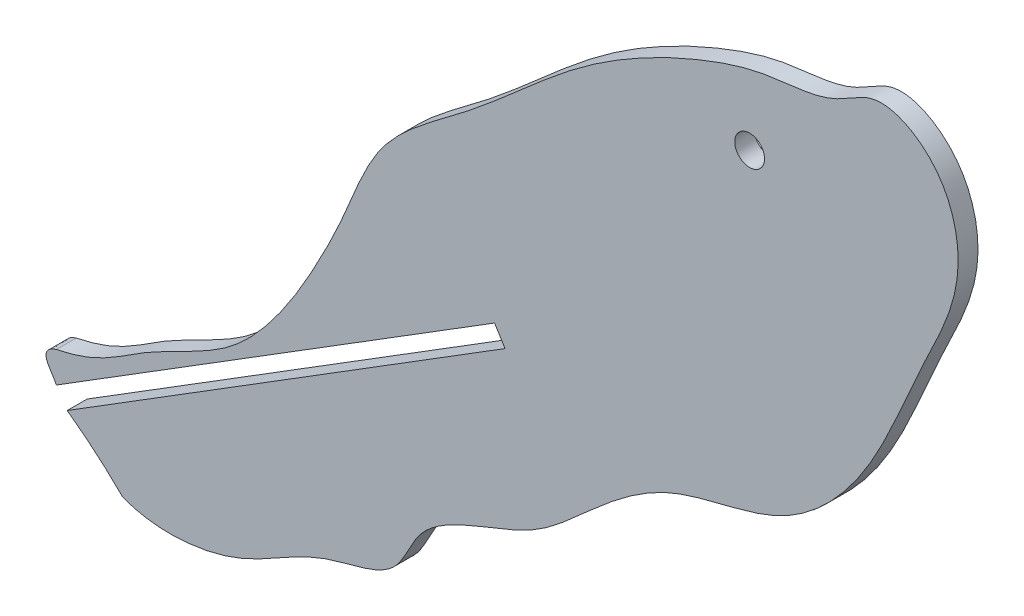
SolidWorks part; units mm, degrees
ref_plane "Front Plane" through (0, 0, 0) normal (0, 0, 1) x (1, 0, 0)
ref_plane "Top Plane" through (0, 0, 0) normal (0, 1, 0) x (1, 0, 0)
ref_plane "Right Plane" through (0, 0, 0) normal (1, 0, 0) x (0, 0, -1)
sketch "Sketch1" plane through (0, 0, 0) normal (0, 0, 1) x (1, 0, 0)
  line L0 (180.8536, 209.2521) -> (904.2678, 209.2521) construction
  line L1 (40.7681, 184.4531) -> (114.0777, 230.0867)
  line L2 (114.0777, 230.0867) -> (115.7555, 227.3912)
  line L3 (115.7555, 227.3912) -> (43.5218, 182.4273)
  circle A0 centre (154.8491, 274.3843) radius 2.3813
  spline S0 degree 3 poles (43.5218, 182.4273) (44.7888, 181.7633) (48.1265, 180.6055) (53.705, 175.7286) (63.3224, 174.3518) (75.4553, 177.0487) (85.4078, 184.7436) (98.3801, 186.1079) (101.4671, 195.5245) (109.9193, 200.5146) (120.6654, 203.617) (130.4193, 213.0619) (142.5491, 222.5703) (160.3937, 224.0819) (174.6413, 238.8523) (181.0537, 256.5862) (190.1561, 272.8659) (186.1713, 287.7244) (175.2422, 293.1031) (167.5413, 286.7867) (157.7282, 286.7768) (143.7964, 282.1538) (126.7856, 272.9997) (111.7023, 257.8497) (95.3696, 247.2825) (90.6008, 233.8212) (85.069, 222.6367) (79.3324, 213.0302) (70.5635, 203.6717) (58.0881, 198.9201) (49.8666, 191.7879) (36.7522, 190.4365) (39.5188, 185.7453) (40.7681, 184.4531) knots 0 0 0 0 0.010738 0.027614 0.053706 0.08047 0.119119 0.148684 0.166042 0.187193 0.219521 0.249445 0.287922 0.333236 0.377489 0.432665 0.476724 0.512866 0.536094 0.553132 0.581565 0.607651 0.663372 0.72474 0.769454 0.804289 0.828955 0.863971 0.888092 0.924485 0.959069 0.980197 0.99194 0.99194 0.99194 0.99194
  dimension "D62" = 4.7625
  dimension "D1" = 38.7108
  dimension "D3" = 46.4081
  dimension "D4" = 47.3137
  dimension "D5" = 52.9734
  dimension "D6" = 58.6332
  dimension "D7" = 63.161
  dimension "D8" = 71.311
  dimension "D9" = 73.5749
  dimension "D10" = 78.1027
  dimension "D11" = 85.5736
  dimension "D12" = 87.3847
  dimension "D13" = 89.875
  dimension "D14" = 95.9876
  dimension "D15" = 98.2515
  dimension "D16" = 101.8737
  dimension "D17" = 108.6654
  dimension "D18" = 109.3446
  dimension "D19" = 120.4377
  dimension "D20" = 128.135
  dimension "D21" = 129.7197
  dimension "D22" = 142.3976
  dimension "D23" = 147.6046
  dimension "D24" = 157.5657
  dimension "D25" = 159.6033
  dimension "D26" = 168.6589
  dimension "D27" = 172.5075
  dimension "D28" = 174.7714
  dimension "D29" = 182.2423
  dimension "D30" = 183.3742
  dimension "D31" = 188.1284
  dimension "D32" = 174.999
  dimension "D33" = 177.0365
  dimension "D34" = 177.2629
  dimension "D35" = 180.6587
  dimension "D37" = 184.0546
  dimension "D38" = 188.5824
  dimension "D39" = 191.9783
  dimension "D40" = 194.4686
  dimension "D41" = 198.3172
  dimension "D42" = 199.4491
  dimension "D43" = 204.6561
  dimension "D44" = 205.3353
  dimension "D45" = 209.2521
  dimension "D46" = 212.127
  dimension "D47" = 220.7298
  dimension "D48" = 223.8993
  dimension "D49" = 226.1632
  dimension "D50" = 232.7285
  dimension "D51" = 238.1619
  dimension "D52" = 245.18
  dimension "D53" = 256.9523
  dimension "D54" = 257.8579
  dimension "D55" = 272.5732
  dimension "D56" = 274.3843
  dimension "D57" = 283.2136
  dimension "D58" = 286.1566
  dimension "D59" = 287.9678
  dimension "D60" = 288.4205
  dimension "D61" = 291.3636
  dimension "D63" = 3.175
  dimension "D64" = 1.5875
extrude "Boss-Extrude1" add sketch "Sketch1" along normal blind 3.175
sketch "Sketch2" plane through (0, 0, 3.175) normal (0, 0, 1) x (1, 0, 0)
  line L0 (115.7555, 227.3912) -> (43.5218, 182.4273) construction
  line L1 (40.7681, 184.4531) -> (114.0777, 230.0867) construction
  line L2 (45.717, 183.7938) -> (44.0391, 186.4892) construction
  line L3 (44.0391, 191.4071) -> (42.3904, 195.3822)
  line L4 (42.3904, 195.3822) -> (32.9994, 190.123)
  line L5 (32.9994, 190.123) -> (39.4136, 174.6588)
  line L6 (39.4136, 174.6588) -> (53.2357, 172.3898)
  line L7 (53.2357, 172.3898) -> (54.6513, 176.2658)
  line L8 (45.77, 183.8267) -> (44.0391, 186.4892)
  line L9 (44.0391, 186.4892) -> (43.8278, 186.7154)
  spline S0 degree 2 poles (54.6513, 176.2658) (50.5119, 180.4057) (45.77, 183.8267) knots 0 0 0 1 1 1
  spline S1 degree 3 poles (43.5218, 182.4273) (44.7888, 181.7633) (48.1265, 180.6055) (53.705, 175.7286) (63.3224, 174.3518) (75.4553, 177.0487) (85.4078, 184.7436) (98.3801, 186.1079) (101.4671, 195.5245) (109.9193, 200.5146) (120.6654, 203.617) (130.4193, 213.0619) (142.5491, 222.5703) (160.3937, 224.0819) (174.6413, 238.8523) (181.0537, 256.5862) (190.1561, 272.8659) (186.1713, 287.7244) (175.2422, 293.1031) (167.5413, 286.7867) (157.7282, 286.7768) (143.7964, 282.1538) (126.7856, 272.9997) (111.7023, 257.8497) (95.3696, 247.2825) (90.6008, 233.8212) (85.069, 222.6367) (79.3324, 213.0302) (70.5635, 203.6717) (58.0881, 198.9201) (49.8666, 191.7879) (36.7522, 190.4365) (39.5188, 185.7453) (40.7681, 184.4531) knots 0 0 0 0 0.010738 0.027614 0.053706 0.08047 0.119119 0.148684 0.166042 0.187193 0.219521 0.249445 0.287922 0.333236 0.377489 0.432665 0.476724 0.512866 0.536094 0.553132 0.581565 0.607651 0.663372 0.72474 0.769454 0.804289 0.828955 0.863971 0.888092 0.924485 0.959069 0.980197 0.99194 0.99194 0.99194 0.99194 construction
  spline S2 degree 3 poles (44.0391, 186.4892) (43.3127, 188.0835) (40.7005, 190.3101) (44.0391, 191.4071) knots 0 0 0 0 1 1 1 1
extrude "Cut-Extrude1" cut sketch "Sketch2" against normal blind 3.175
